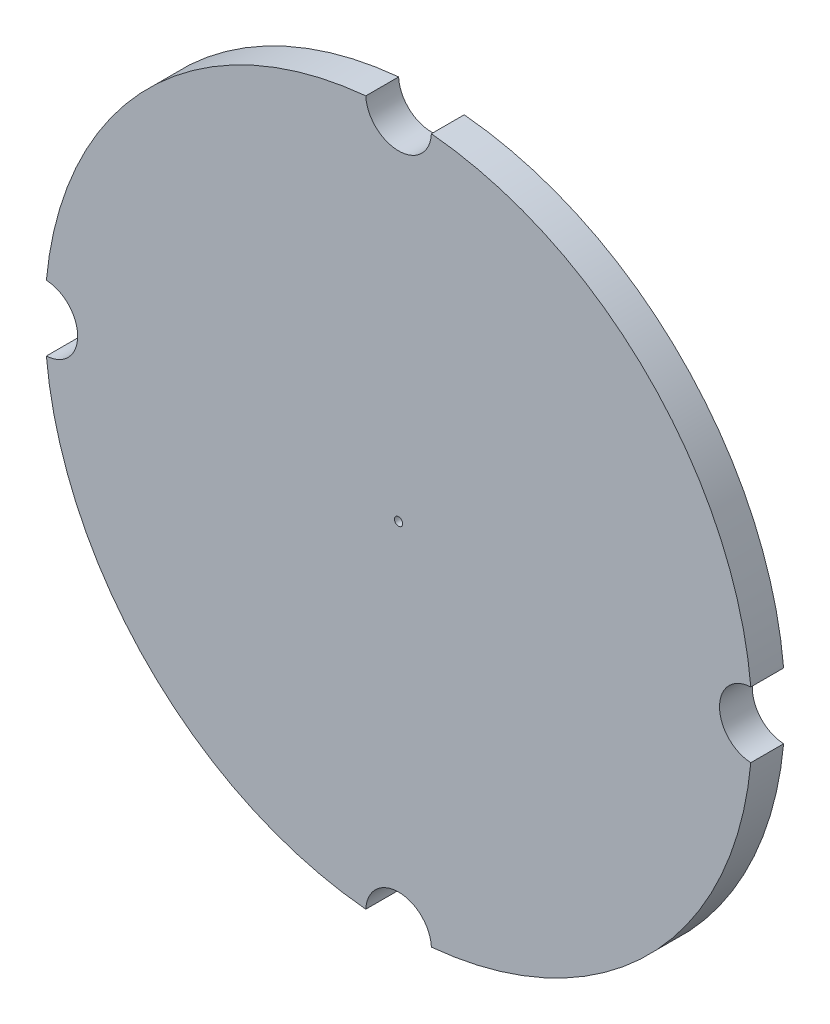
SolidWorks part; units mm, degrees
ref_plane "Front Plane" through (0, 0, 0) normal (0, 0, 1) x (1, 0, 0)
ref_plane "Top Plane" through (0, 0, 0) normal (0, 1, 0) x (1, 0, 0)
ref_plane "Right Plane" through (0, 0, 0) normal (1, 0, 0) x (0, 0, -1)
sketch "Sketch1" plane through (0, 0, 0) normal (0, 0, 1) x (1, 0, 0)
  circle A0 centre (0, 0) radius 215.5261
  circle A1 centre (215.5261, 0) radius 20
  circle A2 centre (0, -215.5261) radius 20
  circle A3 centre (0, -215.5261) radius 20
  circle A4 centre (-215.5261, 0) radius 20
  circle A5 centre (0, 215.5261) radius 20
  circle A6 centre (0, 0) radius 2.5
  point P16 (0, 0)
  dimension "D1" = 40
  dimension "D4" = 5
  dimension "D2" = 304.8
  dimension "D3" = 4
extrude "Boss-Extrude1" add sketch "Sketch1" along normal blind 20 contours A5 A0 A4 A2 A1
sketch "Sketch2" plane through (0, 0, 20) normal (0, 0, 1) x (1, 0, 0)
  line L0 (0, 195.5261) -> (0, 0) construction
  circle A0 centre (0, 0) radius 195.5261 construction
  arc A8 (-19.9785, 214.5982) -> (19.9785, 214.5982) centre (0, 215.5261) ccw
  arc A9 (-19.9785, 214.5982) -> (-214.5982, 19.9785) centre (0, 0) ccw
  arc A10 (-214.5982, -19.9785) -> (-214.5982, 19.9785) centre (-215.5261, 0) ccw
  arc A11 (-214.5982, -19.9785) -> (-19.9785, -214.5982) centre (0, 0) ccw
  arc A12 (19.9785, -214.5982) -> (-19.9785, -214.5982) centre (0, -215.5261) ccw
  arc A13 (19.9785, -214.5982) -> (214.5982, -19.9785) centre (0, 0) ccw
  arc A14 (214.5982, 19.9785) -> (214.5982, -19.9785) centre (215.5261, 0) ccw
  arc A15 (214.5982, 19.9785) -> (19.9785, 214.5982) centre (0, 0) ccw
  arc A16 (-19.9785, 214.5982) -> (19.9785, 214.5982) centre (0, 215.5261) ccw
  arc A17 (-19.9785, 214.5982) -> (-214.5982, 19.9785) centre (0, 0) ccw
  arc A18 (-214.5982, -19.9785) -> (-214.5982, 19.9785) centre (-215.5261, 0) ccw
  arc A19 (-214.5982, -19.9785) -> (-19.9785, -214.5982) centre (0, 0) ccw
  arc A20 (19.9785, -214.5982) -> (-19.9785, -214.5982) centre (0, -215.5261) ccw
  arc A21 (19.9785, -214.5982) -> (214.5982, -19.9785) centre (0, 0) ccw
  arc A22 (214.5982, 19.9785) -> (214.5982, -19.9785) centre (215.5261, 0) ccw
  arc A23 (214.5982, 19.9785) -> (19.9785, 214.5982) centre (0, 0) ccw
  dimension "D1" = 0
